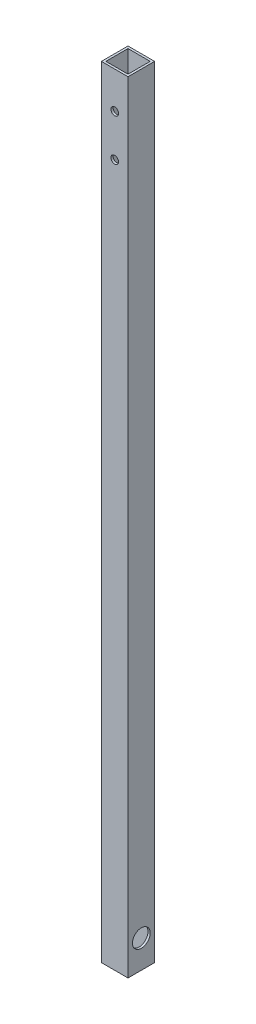
SolidWorks part; units mm, degrees
material "6063-T5"
ref_plane "Front Plane" through (0, 0, 0) normal (0, 0, 1) x (1, 0, 0)
ref_plane "Top Plane" through (0, 0, 0) normal (0, 1, 0) x (1, 0, 0)
ref_plane "Right Plane" through (0, 0, 0) normal (1, 0, 0) x (0, 0, -1)
sketch "Sketch1" plane through (0, 0, 0) normal (0, 1, 0) x (1, 0, 0)
  line L0 (1.5875, 1.5875) -> (17.4625, 1.5875)
  line L5 (0, 0) -> (19.05, 0)
  line L6 (0, 0) -> (0, 19.05)
  line L7 (0, 19.05) -> (19.05, 19.05)
  line L8 (19.05, 0) -> (19.05, 19.05)
  line L9 (17.4625, 1.5875) -> (17.4625, 17.4625)
  line L10 (1.5875, 17.4625) -> (17.4625, 17.4625)
  line L11 (1.5875, 1.5875) -> (1.5875, 17.4625)
  dimension "D1" = 19.05
  dimension "D2" = 19.05
  dimension "D3" = 1.5875
extrude "Boss-Extrude1" add sketch "Sketch1" along normal blind 914.4
sketch "Sketch4" plane through (19.05, 0, 0) normal (1, 0, 0) x (0, 0, -1)
  line L0 (0, 0) -> (19.05, 0) construction
  circle A0 centre (9.525, 20) radius 6.35
  dimension "D2" = 12.7
  dimension "D1" = 20
extrude "Cut-Extrude3" cut sketch "Sketch4" against normal through all
sketch "Sketch5" plane through (0, 0, 0) normal (0, 0, 1) x (1, 0, 0)
  line L0 (19.05, 914.4) -> (19.05, 0) construction
  line L1 (0, 0) -> (19.05, 0)
  line L2 (0, 0) -> (0, 558.8)
  line L3 (0, 558.8) -> (19.05, 558.8)
  line L4 (19.05, 0) -> (19.05, 558.8)
  line L5 (0, 914.4) -> (19.05, 914.4) construction
  dimension "D1" = 355.6
extrude "Cut-Extrude4" cut sketch "Sketch5" against normal through all flip side to cut
sketch "Sketch6" plane through (0, 0, -19.05) normal (0, 0, -1) x (-1, 0, 0)
  line L0 (0, 558.8) -> (0, 0) construction
  line L1 (-19.05, 558.8) -> (0, 558.8) construction
  circle A0 centre (-9.53, 532.6) radius 2.75
  circle A1 centre (-9.53, 502.6) radius 2.75
  dimension "D3" = 5.5
  dimension "D4" = 5.5
  dimension "D1" = 9.53
  dimension "D2" = 9.53
  dimension "D5" = 26.2
  dimension "D6" = 56.2
extrude "Cut-Extrude5" cut sketch "Sketch6" against normal through all
